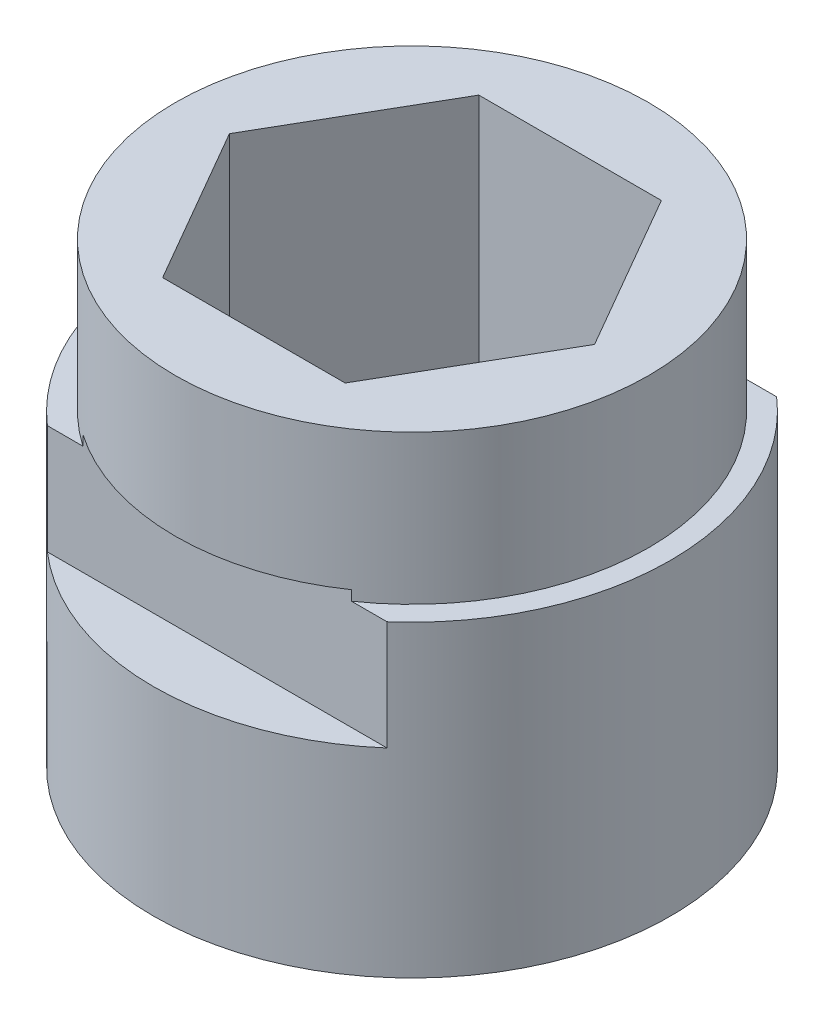
SolidWorks part; units mm, degrees
material "Polyester Resin"
ref_plane "Front Plane" through (0, 0, 0) normal (0, 0, 1) x (1, 0, 0)
ref_plane "Top Plane" through (0, 0, 0) normal (0, 1, 0) x (1, 0, 0)
ref_plane "Right Plane" through (0, 0, 0) normal (1, 0, 0) x (0, 0, -1)
sketch "Sketch1" plane through (0, 0, 0) normal (0, 1, 0) x (1, 0, 0)
  line L1 (-2.9156, 5.05) -> (-5.8312, 0)
  line L2 (-5.8312, 0) -> (-2.9156, -5.05)
  line L3 (-2.9156, -5.05) -> (2.9156, -5.05)
  line L4 (2.9156, -5.05) -> (5.8312, 0)
  line L5 (5.8312, 0) -> (2.9156, 5.05)
  line L6 (2.9156, 5.05) -> (-2.9156, 5.05)
  circle A0 centre (0, 0) radius 5.05 construction
  circle A1 centre (0, 0) radius 7.5565
  dimension "D2" = 15.113
  dimension "D1" = 10.1
extrude "Boss-Extrude1" add sketch "Sketch1" along normal blind 13.97
sketch "Sketch2" plane through (0, 0, 0) normal (0, -1, 0) x (1, 0, 0)
  circle A0 centre (0, 0) radius 7.5565
  circle A1 centre (0, 0) radius 3.3
  dimension "D1" = 6.6
extrude "Boss-Extrude2" add sketch "Sketch2" along normal blind 0.635
sketch "Sketch4" plane through (0, -0.635, 0) normal (0, -1, 0) x (1, 0, 0)
  circle A0 centre (0, 0) radius 7.5565
  circle A1 centre (0, 0) radius 8.255
  dimension "D1" = 16.51
extrude "Boss-Extrude3" add sketch "Sketch4" against normal blind 9.8425
sketch "Sketch3" plane through (0, 0, 0) normal (1, 0, 0) x (0, 0, -1)
  line L0 (-6.223, 9.525) -> (-6.223, 5.715)
  line L1 (6.223, 9.525) -> (6.223, 5.715)
  line L2 (-7.5565, -0.635) -> (7.5565, -0.635) construction
  line L3 (-6.223, 9.525) -> (-8.3636, 9.525)
  line L4 (-8.3636, 9.525) -> (-8.3636, 5.715)
  line L5 (-8.3636, 5.715) -> (-6.223, 5.715)
  line L6 (6.223, 9.525) -> (8.4791, 9.525)
  line L7 (8.4791, 9.525) -> (8.4791, 5.715)
  line L8 (8.4791, 5.715) -> (6.223, 5.715)
  dimension "D1" = 12.446
  dimension "D2" = 6.223
  dimension "D3" = 3.81
  dimension "D4" = 3.81
  dimension "D5" = 6.35
  dimension "D6" = 6.35
extrude "Cut-Extrude1" cut sketch "Sketch3" against normal through all and the other way through all
equation "\"AB_Central_Bushing_Length\" = .75in"
equation "\"Solid_Length\"= .025in"
equation "\"Hex_Length\"=0.55"
equation "\"D1@Boss-Extrude1\"= \"Hex_Length\""
equation "\"D1@Boss-Extrude2\"=\"Solid_Length\""
equation "\"Cutout_Angle\" = 80"
